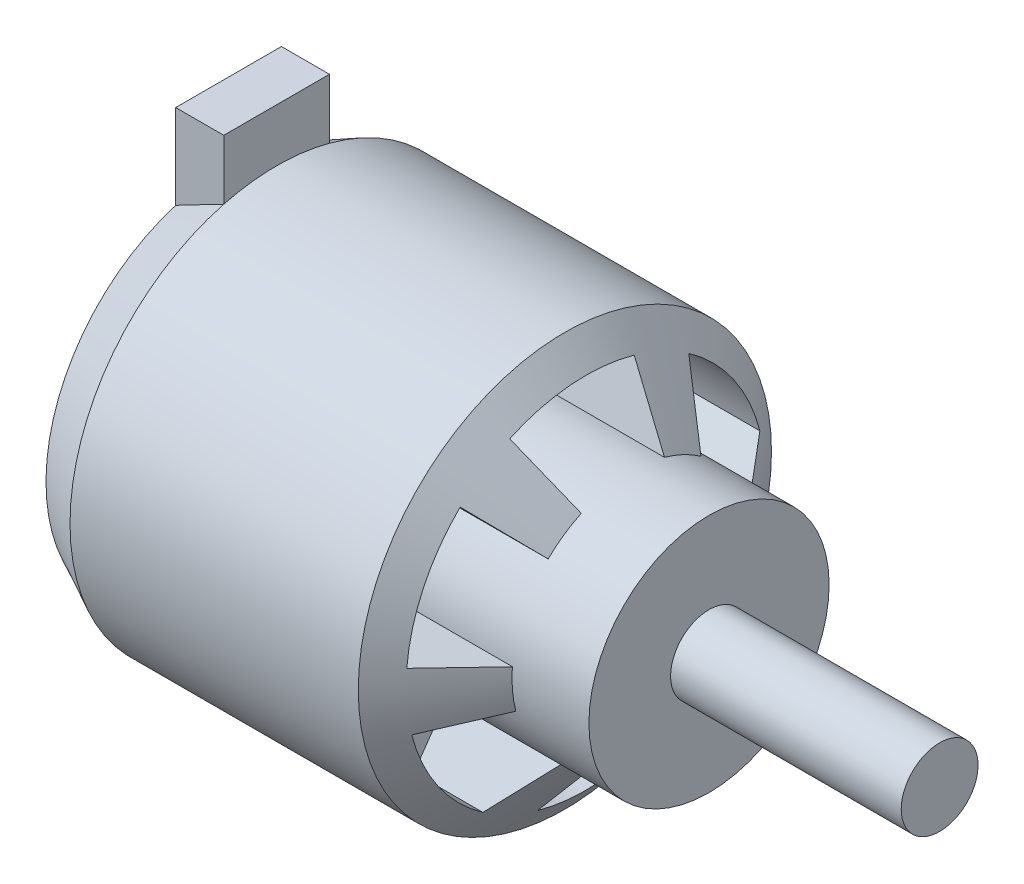
SolidWorks part; units mm, degrees
ref_plane "Front" through (0, 0, 0) normal (0, 0, 1) x (1, 0, 0)
ref_plane "Top" through (0, 0, 0) normal (0, 1, 0) x (1, 0, 0)
ref_plane "Right" through (0, 0, 0) normal (1, 0, 0) x (0, 0, -1)
sketch "Sketch1" plane through (0, 0, 0) normal (0, 0, 1) x (1, 0, 0)
  line L0 (0, 0) -> (0, 19)
  line L1 (0, 19) -> (5, 21.5)
  line L2 (5, 21.5) -> (35, 21.5)
  line L3 (35, 21.5) -> (42, 12.5)
  line L4 (42, 12.5) -> (50, 12.5)
  line L5 (50, 12.5) -> (50, 4)
  line L6 (50, 4) -> (74, 4)
  line L7 (74, 4) -> (74, 0)
  line L8 (0, 0) -> (74, 0) construction
  line L9 (0, 0) -> (74, 0)
  dimension "D1" = 38
  dimension "D2" = 43
  dimension "D3" = 5
  dimension "D4" = 42
  dimension "D5" = 30
  dimension "D6" = 25
  dimension "D7" = 8
  dimension "D8" = 24
  dimension "D9" = 8
revolve "Revolve1" add sketch "Sketch1" angle 360 about L8
sketch "Sketch2" plane through (50, 0, 0) normal (1, 0, 0) x (0, 0, -1)
  line L0 (18.6304, -1.6116) -> (12.4535, -1.0773)
  line L1 (13.078, -13.3662) -> (8.742, -8.9346)
  line L2 (7.9195, -16.9402) -> (5.2938, -11.3237)
  line L3 (-5.0365, -18.009) -> (-3.3666, -12.0381)
  line L4 (-10.7109, -15.3286) -> (-7.1597, -10.2464)
  line L5 (-18.1145, -4.6428) -> (-12.1086, -3.1035)
  line L6 (-18.6304, 1.6116) -> (-12.4535, 1.0773)
  line L7 (-13.078, 13.3662) -> (-8.742, 8.9346)
  line L8 (-7.9195, 16.9402) -> (-5.2938, 11.3237)
  line L9 (5.0365, 18.009) -> (3.3666, 12.0381)
  line L10 (10.7109, 15.3286) -> (7.1597, 10.2464)
  line L11 (18.1145, 4.6428) -> (12.1086, 3.1035)
  circle A0 centre (0, 0) radius 12.5 construction
  arc A1 (8.742, -8.9346) -> (12.4535, -1.0773) centre (0, 0) ccw
  arc A2 (-5.0365, -18.009) -> (7.9195, -16.9402) centre (0, 0) ccw
  arc A3 (-3.3666, -12.0381) -> (5.2938, -11.3237) centre (0, 0) ccw
  circle A4 centre (0, 0) radius 18.7
  arc A5 (13.078, -13.3662) -> (18.6304, -1.6116) centre (0, 0) ccw
  arc A6 (-18.1145, -4.6428) -> (-10.7109, -15.3286) centre (0, 0) ccw
  arc A7 (-12.1086, -3.1035) -> (-7.1597, -10.2464) centre (0, 0) ccw
  arc A8 (-13.078, 13.3662) -> (-18.6304, 1.6116) centre (0, 0) ccw
  arc A9 (-8.742, 8.9346) -> (-12.4535, 1.0773) centre (0, 0) ccw
  arc A10 (5.0365, 18.009) -> (-7.9195, 16.9402) centre (0, 0) ccw
  arc A11 (3.3666, 12.0381) -> (-5.2938, 11.3237) centre (0, 0) ccw
  arc A12 (18.1145, 4.6428) -> (10.7109, 15.3286) centre (0, 0) ccw
  arc A13 (12.1086, 3.1035) -> (7.1597, 10.2464) centre (0, 0) ccw
  point P31 (0, 0)
  dimension "D2" = 13
  dimension "D1" = 2.8
  dimension "D3" = 6
extrude "Cut-Extrude1" cut sketch "Sketch2" against normal blind 20
sketch "Sketch3" plane through (0, 0, 0) normal (0, 1, 0) x (1, 0, 0)
  line L0 (0, 19) -> (0, -19) construction
  line L1 (0, 5.5) -> (5, 5.5)
  line L2 (0, 5.5) -> (0, -5.5)
  line L3 (0, -5.5) -> (5, -5.5)
  line L4 (5, 5.5) -> (5, -5.5)
  line L5 (5, -21.5) -> (5, 21.5) construction
  line L6 (5, 0) -> (0, 0) construction
  line L7 (5, -21.5) -> (35, -21.5) construction
  line L8 (35, 21.5) -> (5, 21.5) construction
  dimension "D1" = 11
extrude "Boss-Extrude1" add sketch "Sketch3" along normal blind 27
sketch "Sketch4" plane through (0, 0, 0) normal (-1, 0, 0) x (0, 0, 1)
  circle A0 centre (0, 0) radius 12.35 construction
  circle A1 centre (0, 12.35) radius 1.5
  circle A2 centre (12.35, 0) radius 1.5
  circle A3 centre (0, -12.35) radius 1.5
  circle A4 centre (-12.35, 0) radius 1.5
  point P14 (0, 0)
  dimension "D1" = 24.7
  dimension "D2" = 3
  dimension "D3" = 4
extrude "Cut-Extrude2" cut sketch "Sketch4" against normal blind 5
